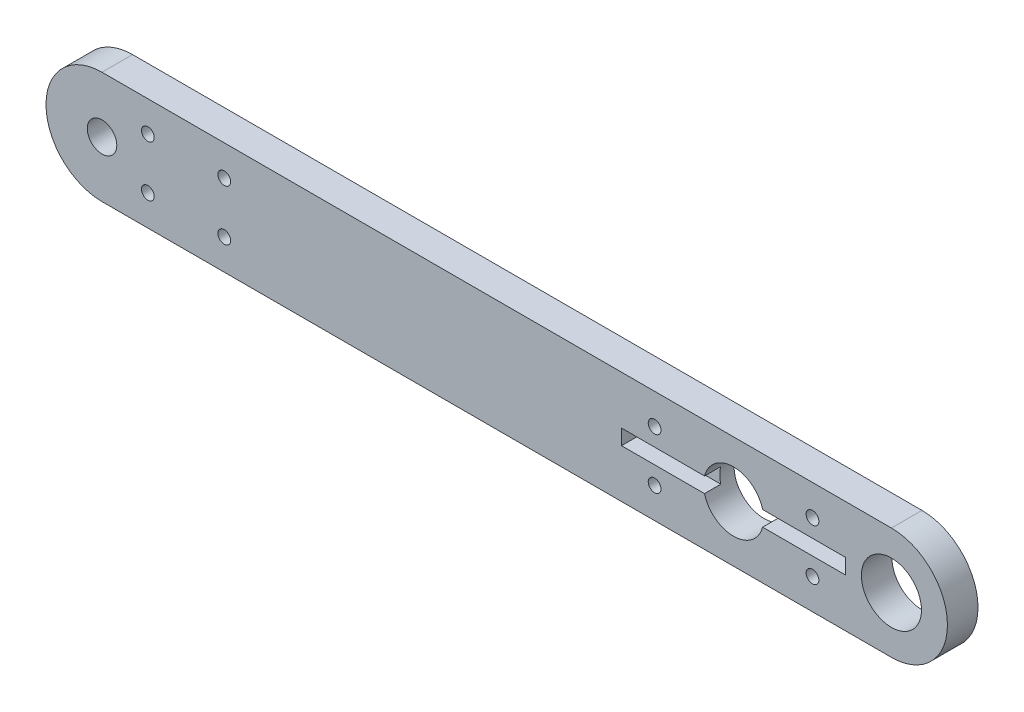
SolidWorks part; units mm, degrees
material "POM copolymère d'acétal"
ref_plane "Front Plane" through (0, 0, 0) normal (0, 0, 1) x (1, 0, 0)
ref_plane "Top Plane" through (0, 0, 0) normal (0, 1, 0) x (1, 0, 0)
ref_plane "Right Plane" through (0, 0, 0) normal (1, 0, 0) x (0, 0, -1)
sketch "Sketch1" plane through (0, 0, 0) normal (0, 0, 1) x (1, 0, 0)
  line L0 (15.5, 5.5) -> (-62, 5.5)
  line L1 (-62, -5.5) -> (15.5, -5.5)
  line L2 (0, 0) -> (31.9738, 0) construction
  arc A0 (-62, 5.5) -> (-62, -5.5) centre (-62, 0) ccw
  arc A1 (15.5, -5.5) -> (15.5, 5.5) centre (15.5, 0) ccw
  circle A2 centre (-62, 0) radius 1.45
  circle A3 centre (0, 0) radius 2.95
  circle A4 centre (15.5, 0) radius 2.95
  dimension "D1" = 5.9
  dimension "D2" = 15.5
  dimension "D3" = 2.9
  dimension "D4" = 62
  dimension "D5" = 5.5
  dimension "D6" = 5.9
extrude "Boss-Extrude1" add sketch "Sketch1" along normal blind 3
hole_wizard "Trou taraudé M1.61" positions "Sketch3" profile "Sketch2" tap size "M1.6" standard "Iso" end condition through all
sketch "Sketch3" plane through (0, 0, 3) normal (0, 0, 1) x (1, 0, 0)
  line L0 (0, 0) -> (-68.8863, 0) construction
  line L2 (7.75, -12.0598) -> (7.75, 13.3437) construction
  line L4 (0, 0) -> (0, 9.9697) construction
  circle A0 centre (-62, 0) radius 1.45 construction
  circle A1 centre (0, 0) radius 2.95 construction
  circle A2 centre (15.5, 0) radius 2.95 construction
  point P1 (7.75, 2.5)
  point P5 (-7.75, 2.5)
  point P7 (-57.5, 2.5)
  point P11 (-50, 2.5)
  dimension "D1" = 4.5
  dimension "D2" = 12
  dimension "D3" = 5
sketch "Sketch2" plane through (7.75, 2.5, 3) normal (1, 0, 0) x (0, -1, 0)
  line L0 (0, 0) -> (0, 3)
  line L1 (0, 3) -> (0.625, 3)
  line L2 (0.625, 3) -> (0.625, 0)
  line L5 (0.625, 0) -> (0, 0)
  line L11 (0, -6.35) -> (0, 107.95) construction
  dimension "Diamètre principal du filetage" = 1.25
  dimension "Profondeur du trou pour taraudage jusqu'au prochain" = 3
mirror "Mirror1" about plane through (0, 0, 0) normal (0, 1, 0) of "Trou taraudé M1.61"
sketch "Esquisse3" plane through (0, 0, 3) normal (0, 0, 1) x (1, 0, 0)
  line L1 (-11, 0.75) -> (11, 0.75)
  line L2 (-11, 0.75) -> (-11, -0.75)
  line L3 (-11, -0.75) -> (11, -0.75)
  line L4 (11, 0.75) -> (11, -0.75)
  dimension "D1" = 0.75
  dimension "D2" = 1.5
  dimension "D3" = 11
  dimension "D4" = 22
extrude "Enlèv. mat.-Extru.1" cut sketch "Esquisse3" against normal blind 1.6
